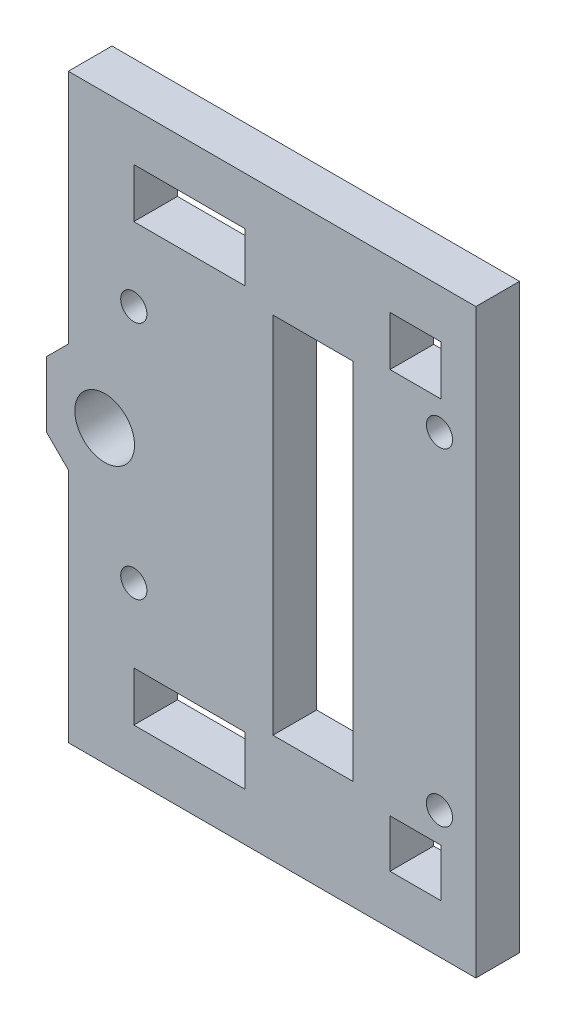
SolidWorks part; units mm, degrees
ref_plane "Plano frontal" through (0, 0, 0) normal (0, 0, 1) x (1, 0, 0)
ref_plane "Plano superior" through (0, 0, 0) normal (0, 1, 0) x (1, 0, 0)
ref_plane "Plano direito" through (0, 0, 0) normal (1, 0, 0) x (0, 0, -1)
sketch "Model" plane through (0, 0, 0) normal (0, 0, 1) x (1, 0, 0)
  line L0 (69.7947, 71.5746) -> (69.7947, 21.5746)
  line L1 (30.6773, 6.6246) -> (30.6773, 39.0855)
  line L2 (30.6773, 86.5246) -> (86.6773, 86.5246)
  line L3 (86.6773, 86.5246) -> (86.6773, 6.6246)
  line L4 (86.6773, 6.6246) -> (30.6773, 6.6246)
  line L5 (30.6773, 54.0637) -> (30.6773, 86.5246)
  line L6 (27.6773, 51.0637) -> (30.6773, 54.0637)
  line L7 (27.6773, 51.0637) -> (27.6773, 42.0855)
  line L8 (27.6773, 42.0855) -> (30.6773, 39.0855)
  line L9 (69.7947, 21.5746) -> (58.7947, 21.5746)
  line L10 (58.7947, 21.5746) -> (58.7947, 71.5746)
  line L11 (58.7947, 71.5746) -> (69.7947, 71.5746)
  line L12 (81.8773, 13.4246) -> (81.8773, 20.0246)
  line L13 (74.8773, 13.4246) -> (81.8773, 13.4246)
  line L14 (74.8773, 20.0246) -> (74.8773, 13.4246)
  line L15 (81.8773, 20.0246) -> (74.8773, 20.0246)
  line L16 (39.6773, 20.0246) -> (39.6773, 13.2246)
  line L17 (54.9895, 20.0246) -> (39.6773, 20.0246)
  line L18 (54.9895, 13.2246) -> (54.9895, 20.0246)
  line L19 (39.6773, 13.2246) -> (54.9895, 13.2246)
  line L20 (39.6773, 73.1246) -> (39.6773, 79.9246)
  line L21 (39.6773, 79.9246) -> (54.9895, 79.9246)
  line L22 (54.9895, 79.9246) -> (54.9895, 73.1246)
  line L23 (54.9895, 73.1246) -> (39.6773, 73.1246)
  line L24 (81.8773, 73.1246) -> (74.8773, 73.1246)
  line L25 (74.8773, 73.1246) -> (74.8773, 79.9246)
  line L26 (74.8773, 79.9246) -> (81.8773, 79.9246)
  line L27 (81.8773, 79.9246) -> (81.8773, 73.1246)
  circle A0 centre (81.6773, 24.0746) radius 1.8
  circle A1 centre (39.6773, 30.1246) radius 1.8
  circle A2 centre (35.6773, 46.5746) radius 4.1
  circle A3 centre (39.6773, 63.0246) radius 1.8
  circle A4 centre (81.6773, 69.0746) radius 1.8
extrude "Ressalto-extrusão1" add sketch "Model" along normal blind 6
ref_plane "Plano1" through (0, 16.7246, 0) normal (0, -1, 0) x (-1, 0, 0)
ref_plane "Plano2" through (0, 76.5246, 0) normal (0, 1, 0) x (1, 0, 0)
ref_plane "Plano3" through (60.7773, 0, 0) normal (1, 0, 0) x (0, 0, -1)
ref_plane "Plano4" through (64.2947, 0, 0) normal (-1, 0, 0) x (0, 0, 1)
